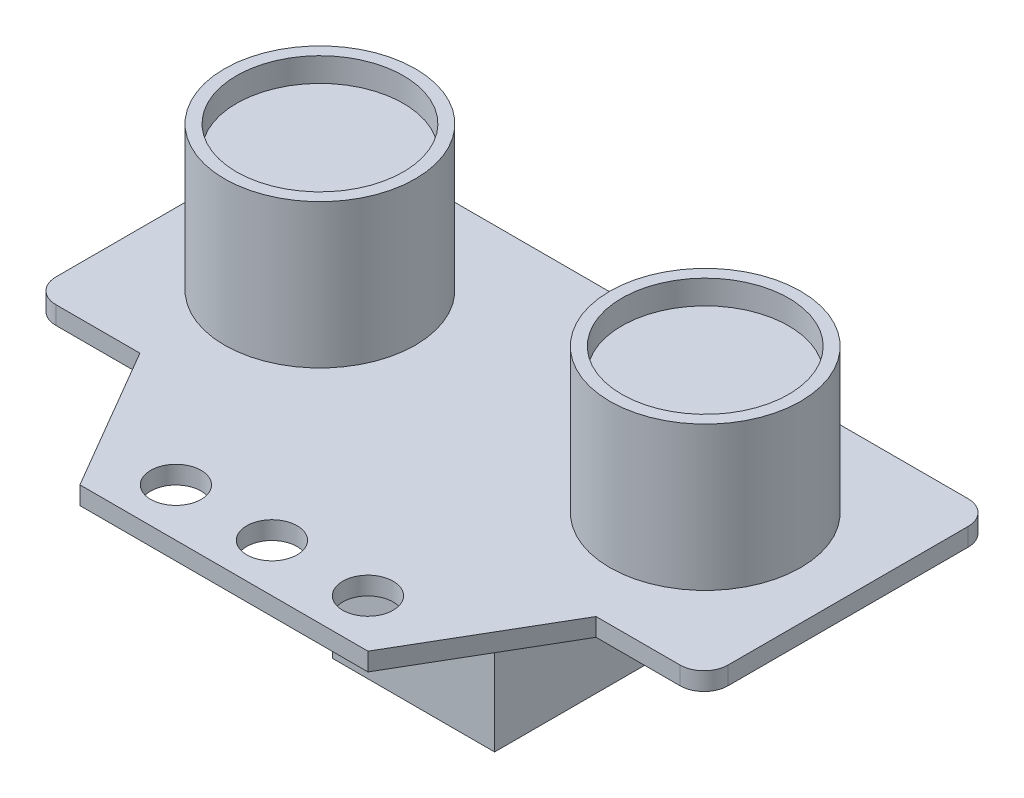
SolidWorks part; units mm, degrees
ref_plane "Front Plane" through (0, 0, 0) normal (0, 0, 1) x (1, 0, 0)
ref_plane "Top Plane" through (0, 0, 0) normal (0, 1, 0) x (1, 0, 0)
ref_plane "Right Plane" through (0, 0, 0) normal (1, 0, 0) x (0, 0, -1)
sketch "Sketch1" plane through (0, 0, 0) normal (0, 1, 0) x (1, 0, 0)
  line L0 (12, 0) -> (-12, 0)
  line L1 (-12, 0) -> (-19, 12)
  line L2 (-19, 12) -> (-28, 12)
  line L3 (-28, 12) -> (-28, 36)
  line L4 (-28, 36) -> (28, 36)
  line L5 (0, 36) -> (0, 0) construction
  line L6 (28, 12) -> (28, 36)
  line L7 (19, 12) -> (28, 12)
  line L8 (12, 0) -> (19, 12)
  line L9 (-8, 4) -> (8, 4) construction
  circle A0 centre (0, 4) radius 2.1
  circle A1 centre (-8, 4) radius 2.1
  circle A2 centre (8, 4) radius 2.1
  dimension "D6" = 4.2
  dimension "D1" = 56
  dimension "D2" = 36
  dimension "D3" = 24
  dimension "D4" = 24
  dimension "D5" = 9
  dimension "D7" = 1.9
  dimension "D8" = 16
extrude "Boss-Extrude1" add sketch "Sketch1" along normal blind 1.5
fillet "Fillet1" radius 2 4 edges at (28, 0.75, -12) (28, 0.75, -36) (-28, 0.75, -36) (-28, 0.75, -12)
sketch "Sketch2" plane through (0, 1.5, 0) normal (0, 1, 0) x (1, 0, 0)
  line L0 (0, 0) -> (0, 36) construction
  line L1 (26, 36) -> (-26, 36) construction
  line L2 (-28, 34) -> (-28, 14) construction
  circle A0 centre (-16.05, 24.05) radius 7.95
  circle A1 centre (16.05, 24.05) radius 7.95
  dimension "D1" = 15.9
  dimension "D2" = 4
  dimension "D3" = 4
extrude "Boss-Extrude2" add sketch "Sketch2" along normal blind 12
sketch "Sketch3" plane through (0, 0, 0) normal (0, -1, 0) x (1, 0, 0)
  line L0 (26, -36) -> (-26, -36) construction
  line L1 (-6.75, -15.8) -> (6.75, -15.8)
  line L2 (-6.75, -15.8) -> (-6.75, -31.8)
  line L3 (-6.75, -31.8) -> (6.75, -31.8)
  line L4 (6.75, -15.8) -> (6.75, -31.8)
  point P4 (0, -15.8)
  dimension "D1" = 13.5
  dimension "D2" = 16
  dimension "D3" = 4.2
extrude "Boss-Extrude3" add sketch "Sketch3" along normal blind 16.3
sketch "Sketch4" plane through (0, 13.5, 0) normal (0, 1, 0) x (1, 0, 0)
  circle A3 centre (-16.05, 24.05) radius 6.95
  circle A4 centre (-16.05, 24.05) radius 6.95
  circle A6 centre (16.05, 24.05) radius 6.95
  circle A7 centre (16.05, 24.05) radius 6.95
  dimension "D1" = 1
  dimension "D2" = 1
extrude "Cut-Extrude1" cut sketch "Sketch4" against normal blind 2
equation "\"width\"= 24"
equation "\"thk\"= 3"
equation "\"holesize\"= 4.2"
equation "\"holedistance\"= ( 20 + 12 ) / 2"
equation "\"threaded_hole\"= 3.9"
equation "\"fillet_radius\"= 2"
equation "\"ground_clearance\"= 25"
equation "\"tire_thk\"= 3"
equation "\"innerwheel_diam\" = \"wheel_diam\"-2*\"tire_thk\""
equation "\"innerwheel_thk\"= 8"
equation "\"wheel_diam\"= 2*(\"width\"/2+\"ground_clearance\")"
equation "\"D6@Sketch1\"=\"holesize\""
equation "\"D8@Sketch1\"=\"holedistance\""
equation "\"coloursensor_holesize\"= 2.65"
equation "\"hole_to_edge\" = 4"
